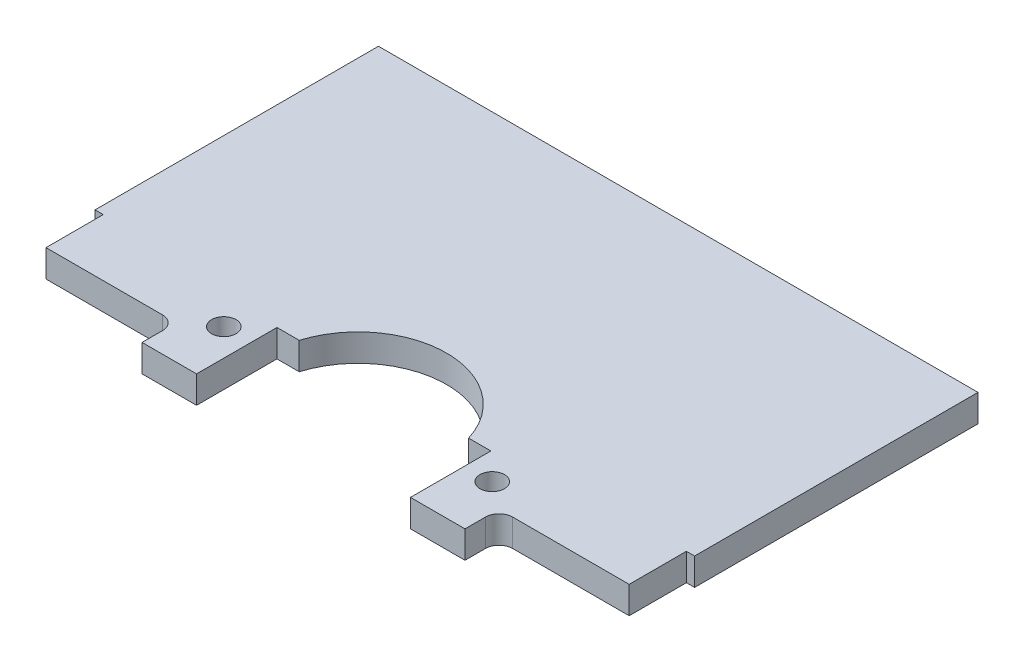
SolidWorks part; units mm, degrees
ref_plane "Front Plane" through (0, 0, 0) normal (0, 0, 1) x (1, 0, 0)
ref_plane "Top Plane" through (0, 0, 0) normal (0, 1, 0) x (1, 0, 0)
ref_plane "Right Plane" through (0, 0, 0) normal (1, 0, 0) x (0, 0, -1)
sketch "Sketch1" plane through (0, 0, 0) normal (0, 1, 0) x (1, 0, 0)
  line L0 (0, 0) -> (0, -20.1295) construction
  line L1 (-27.94, -13.208) -> (27.94, -13.208)
  line L2 (-27.94, -13.208) -> (-27.94, 13.208)
  line L3 (-27.94, 13.208) -> (27.94, 13.208)
  line L4 (27.94, -13.208) -> (27.94, 13.208)
  line L5 (-27.94, -13.208) -> (27.94, 13.208) construction
  line L6 (-27.94, 13.208) -> (27.94, -13.208) construction
  line L7 (-9.9695, -21.717) -> (-9.9695, -14.224)
  line L8 (-27.178, -18.542) -> (27.178, -18.542)
  line L9 (-27.178, -18.542) -> (-27.178, -13.208)
  line L10 (-27.178, -13.208) -> (27.178, -13.208)
  line L11 (27.178, -18.542) -> (27.178, -13.208)
  line L12 (-27.178, -18.542) -> (27.178, -13.208) construction
  line L13 (-27.178, -13.208) -> (27.178, -18.542) construction
  line L14 (-15.0495, -21.717) -> (15.0495, -21.717)
  line L15 (-15.0495, -21.717) -> (-15.0495, -18.542)
  line L16 (-15.0495, -18.542) -> (15.0495, -18.542)
  line L17 (15.0495, -21.717) -> (15.0495, -18.542)
  line L18 (-15.0495, -21.717) -> (15.0495, -18.542) construction
  line L19 (-15.0495, -18.542) -> (15.0495, -21.717) construction
  line L20 (-9.9695, -14.224) -> (9.9695, -14.224)
  line L21 (9.9695, -14.224) -> (9.9695, -21.717)
  line L22 (-12.5095, -21.717) -> (-12.5095, -16.637) construction
  line L23 (12.5095, -21.717) -> (12.5095, -16.637) construction
  line L24 (-12.5095, -16.637) -> (12.5095, -16.637) construction
  circle A0 centre (-12.5095, -16.637) radius 1.143
  circle A1 centre (12.5095, -16.637) radius 1.143
  arc A2 (-7.8945, -14.224) -> (7.8945, -14.224) centre (0, -16.637) cw
  point P0 (0, 0)
  point P8 (0, -15.875)
  dimension "D11" = 2.286
  dimension "D12" = 8.255
  dimension "D1" = 55.88
  dimension "D2" = 26.416
  dimension "D3" = 31.75
  dimension "D4" = 0.762
  dimension "D5" = 34.925
  dimension "D6" = 27.432
  dimension "D7" = 19.939
  dimension "D8" = 5.08
  dimension "D9" = 2.54
  dimension "D10" = 5.08
extrude "body" add sketch "Sketch1" along normal blind 2.54 contours L1 A2 L4 L3 L2 | L20 A2 L1 L9 L8 L7 A0 | L1 A2 L20 L21 L16 L8 L11 A1 | L15 L14 L7 L8 | L16 L21 L14 L17
fillet "Fillet1" radius 1.27 2 edges at (-15.0495, 1.27, 18.542) (15.0495, 1.27, 18.542)
sketch "base curves" plane through (0, 2.54, 0) normal (0, 1, 0) x (1, 0, 0)
  line L0 (0, 0) -> (0, -16.637) construction
  line L1 (0, -16.637) -> (-34.1415, 17.5045) construction
  line L2 (0, -16.637) -> (35.5103, 18.8733) construction
  line L3 (0, -16.637) -> (32.0915, 18.3847) construction
  line L14 (39.0872, 398.9258) -> (397.426, 414.258) construction
  line L31 (-27.94, -13.208) -> (-27.178, -13.208)
  line L32 (-27.178, -13.208) -> (-27.178, -18.542)
  line L33 (-27.178, -18.542) -> (-16.3195, -18.542)
  line L34 (-15.0495, -19.812) -> (-15.0495, -21.717)
  line L35 (-15.0495, -21.717) -> (-9.9695, -21.717)
  line L36 (-9.9695, -21.717) -> (-9.9695, -14.224)
  line L37 (-9.9695, -14.224) -> (-7.8945, -14.224)
  line L38 (7.8945, -14.224) -> (9.9695, -14.224)
  line L39 (9.9695, -14.224) -> (9.9695, -21.717)
  line L40 (9.9695, -21.717) -> (15.0495, -21.717)
  line L41 (15.0495, -21.717) -> (15.0495, -19.812)
  line L42 (16.3195, -18.542) -> (27.178, -18.542)
  line L43 (27.178, -18.542) -> (27.178, -13.208)
  line L44 (27.178, -13.208) -> (27.94, -13.208)
  line L45 (27.94, -13.208) -> (27.94, 13.208)
  line L46 (27.94, 13.208) -> (-27.94, 13.208)
  line L47 (-27.94, 13.208) -> (-27.94, -13.208)
  line L48 (-27.94, -13.208) -> (-27.178, -13.208)
  line L49 (-27.178, -13.208) -> (-27.178, -18.542)
  line L50 (-27.178, -18.542) -> (-16.3195, -18.542)
  line L51 (-15.0495, -19.812) -> (-15.0495, -21.717)
  line L52 (-15.0495, -21.717) -> (-9.9695, -21.717)
  line L53 (-9.9695, -21.717) -> (-9.9695, -14.224)
  line L54 (-9.9695, -14.224) -> (-7.8945, -14.224)
  line L55 (7.8945, -14.224) -> (9.9695, -14.224)
  line L56 (9.9695, -14.224) -> (9.9695, -21.717)
  line L57 (9.9695, -21.717) -> (15.0495, -21.717)
  line L58 (15.0495, -21.717) -> (15.0495, -19.812)
  line L59 (16.3195, -18.542) -> (27.178, -18.542)
  line L60 (27.178, -18.542) -> (27.178, -13.208)
  line L61 (27.178, -13.208) -> (27.94, -13.208)
  line L62 (27.94, -13.208) -> (27.94, 13.208)
  line L63 (27.94, 13.208) -> (-27.94, 13.208)
  line L64 (-27.94, 13.208) -> (-27.94, -13.208)
  arc A0 (-15.0616, -1.5754) -> (14.1756, -1.1671) centre (0, -33.0858) cw
  arc A1 (-17.6451, 1.0081) -> (16.632, 1.5136) centre (0, -33.0858) cw
  arc A2 (-18.4283, 1.7913) -> (17.3771, 2.3267) centre (0, -33.0858) cw
  arc A4 (-16.2205, -0.4165) -> (15.2772, 0.0352) centre (0, -33.0858) cw
  circle A5 centre (-12.5095, -16.637) radius 1.143 construction
  circle A6 centre (12.5095, -16.637) radius 1.143 construction
  circle A7 centre (-12.5095, -16.637) radius 1.143
  arc A8 (-15.0495, -19.812) -> (-16.3195, -18.542) centre (-16.3195, -19.812) ccw
  arc A9 (7.8945, -14.224) -> (-7.8945, -14.224) centre (0, -16.637) ccw
  arc A10 (16.3195, -18.542) -> (15.0495, -19.812) centre (16.3195, -19.812) ccw
  arc A11 (-15.0495, -19.812) -> (-16.3195, -18.542) centre (-16.3195, -19.812) ccw
  arc A12 (7.8945, -14.224) -> (-7.8945, -14.224) centre (0, -16.637) ccw
  arc A13 (16.3195, -18.542) -> (15.0495, -19.812) centre (16.3195, -19.812) ccw
  circle A14 centre (12.5095, -16.637) radius 1.143
  point P4 (17.3771, 2.3267)
  point P8 (16.632, 1.5136)
  point P9 (15.2772, 0.0352)
  dimension "D1" = 34.925
  dimension "D3" = 16.4488
  dimension "D6" = 36.4746
  dimension "D7" = 38.3894
  dimension "D8" = 39.4463
  dimension "D5" = 2.5
  dimension "D2" = 45
  dimension "D4" = 90
  dimension "D17" = 0
sketch "hours" plane through (0, 0, 0) normal (0, 1, 0) x (1, 0, 0)
  line L0 (-18.4283, 1.7913) -> (-16.2205, -0.4165)
  line L1 (-14.7004, 2.3774) -> (-13.4845, 0.8046)
  line L2 (-11.7915, 3.4478) -> (-10.7971, 1.754)
  line L3 (-9.3419, 5.2383) -> (-8.1575, 2.4648)
  line L4 (-6.0847, 4.8183) -> (-5.5585, 2.9627)
  line L5 (-3.2743, 5.1637) -> (-2.9893, 3.266)
  line L6 (-0.5017, 6.3573) -> (-0.4369, 3.3861)
  line L7 (2.3148, 5.2337) -> (2.113, 3.3275)
  line L8 (5.1188, 4.9608) -> (4.6749, 3.0879)
  line L9 (8.3215, 5.4728) -> (7.2623, 2.6584)
  line L10 (10.8031, 3.7522) -> (9.887, 2.0231)
  line L11 (13.6988, 2.7763) -> (12.5575, 1.1589)
  line L12 (17.3771, 2.3267) -> (15.2772, 0.0352)
  line L17 (-9.9695, -14.224) -> (-7.8945, -14.224)
  line L18 (7.8945, -14.224) -> (9.9695, -14.224)
  line L19 (9.9695, -14.224) -> (9.9695, -21.717)
  line L20 (9.9695, -21.717) -> (15.0495, -21.717)
  line L21 (15.0495, -21.717) -> (15.0495, -19.812)
  line L22 (16.3195, -18.542) -> (27.178, -18.542)
  line L23 (27.178, -18.542) -> (27.178, -13.208)
  line L24 (27.178, -13.208) -> (27.94, -13.208)
  line L25 (27.94, -13.208) -> (27.94, 13.208)
  line L26 (27.94, 13.208) -> (-27.94, 13.208)
  line L27 (-27.94, 13.208) -> (-27.94, -13.208)
  line L28 (-27.94, -13.208) -> (-27.178, -13.208)
  line L29 (-27.178, -13.208) -> (-27.178, -18.542)
  line L30 (-27.178, -18.542) -> (-16.3195, -18.542)
  line L31 (-15.0495, -19.812) -> (-15.0495, -21.717)
  line L32 (-15.0495, -21.717) -> (-9.9695, -21.717)
  line L33 (-9.9695, -21.717) -> (-9.9695, -14.224)
  line L34 (-9.9695, -14.224) -> (-7.8945, -14.224)
  line L35 (7.8945, -14.224) -> (9.9695, -14.224)
  line L36 (9.9695, -14.224) -> (9.9695, -21.717)
  line L37 (9.9695, -21.717) -> (15.0495, -21.717)
  line L38 (15.0495, -21.717) -> (15.0495, -19.812)
  line L39 (16.3195, -18.542) -> (27.178, -18.542)
  line L40 (27.178, -18.542) -> (27.178, -13.208)
  line L41 (27.178, -13.208) -> (27.94, -13.208)
  line L42 (27.94, -13.208) -> (27.94, 13.208)
  line L43 (27.94, 13.208) -> (-27.94, 13.208)
  line L44 (-27.94, 13.208) -> (-27.94, -13.208)
  line L45 (-27.94, -13.208) -> (-27.178, -13.208)
  line L46 (-27.178, -13.208) -> (-27.178, -18.542)
  line L47 (-27.178, -18.542) -> (-16.3195, -18.542)
  line L48 (-15.0495, -19.812) -> (-15.0495, -21.717)
  line L49 (-15.0495, -21.717) -> (-9.9695, -21.717)
  line L50 (-9.9695, -21.717) -> (-9.9695, -14.224)
  arc A0 (15.2772, 0.0352) -> (-16.2205, -0.4165) centre (0, -33.0858) ccw construction
  circle A1 centre (12.5095, -16.637) radius 1.143
  circle A2 centre (12.5095, -16.637) radius 1.143
  arc A3 (7.8945, -14.224) -> (-7.8945, -14.224) centre (0, -16.637) ccw
  arc A4 (16.3195, -18.542) -> (15.0495, -19.812) centre (16.3195, -19.812) ccw
  arc A5 (-15.0495, -19.812) -> (-16.3195, -18.542) centre (-16.3195, -19.812) ccw
  arc A6 (7.8945, -14.224) -> (-7.8945, -14.224) centre (0, -16.637) ccw
  arc A7 (16.3195, -18.542) -> (15.0495, -19.812) centre (16.3195, -19.812) ccw
  arc A8 (-15.0495, -19.812) -> (-16.3195, -18.542) centre (-16.3195, -19.812) ccw
  circle A9 centre (-12.5095, -16.637) radius 1.143
  circle A10 centre (-12.5095, -16.637) radius 1.143
  arc A11 (17.3771, 2.3267) -> (-18.4283, 1.7913) centre (0, -33.0858) ccw construction
  arc A12 (16.632, 1.5136) -> (-17.6451, 1.0081) centre (0, -33.0858) ccw construction
  arc A13 (14.1756, -1.1671) -> (-15.0616, -1.5754) centre (0, -33.0858) ccw construction
  arc A14 (15.2772, 0.0352) -> (-16.2205, -0.4165) centre (0, -33.0858) ccw
  arc A15 (17.3771, 2.3267) -> (-18.4283, 1.7913) centre (0, -33.0858) ccw
  arc A16 (16.632, 1.5136) -> (-17.6451, 1.0081) centre (0, -33.0858) ccw
  arc A17 (14.1756, -1.1671) -> (-15.0616, -1.5754) centre (0, -33.0858) ccw
  point P59 (-29.8291, 7.7981)
  dimension "D1" = 0
  dimension "D2" = 0
  dimension "D3" = 0
